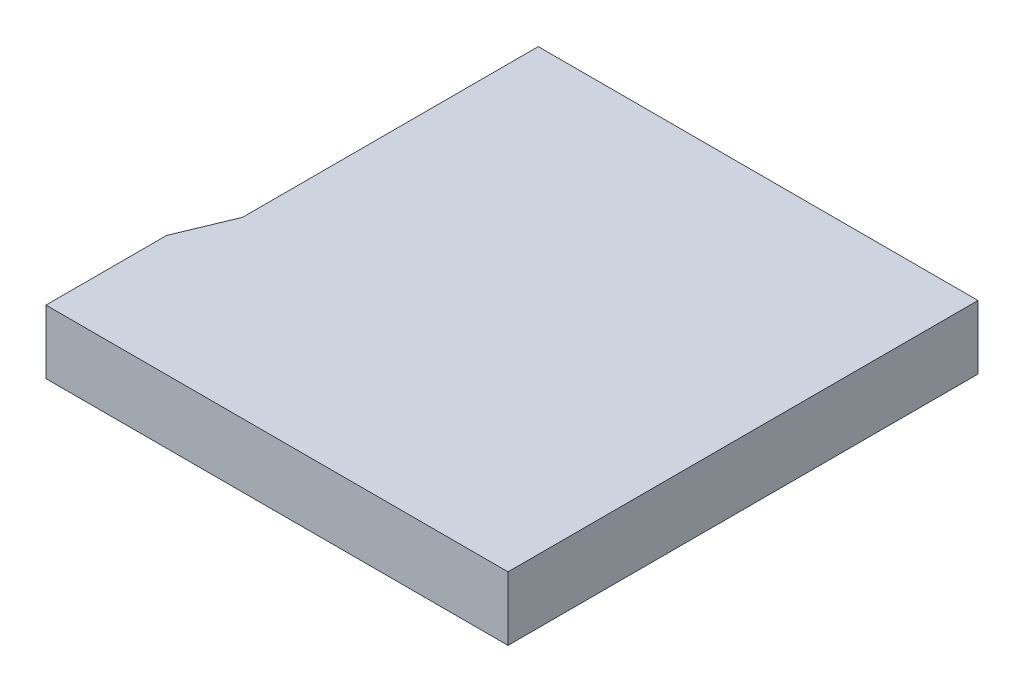
SolidWorks part; units mm, degrees
ref_plane "Спереди" through (0, 0, 0) normal (0, 0, 1) x (1, 0, 0)
ref_plane "Сверху" through (0, 0, 0) normal (0, 1, 0) x (1, 0, 0)
ref_plane "Справа" through (0, 0, 0) normal (1, 0, 0) x (0, 0, -1)
sketch "Эскиз1" plane through (0, 0, 0) normal (0, 1, 0) x (1, 0, 0)
  line L0 (0, 0) -> (14.5, 0)
  line L1 (14.5, 0) -> (14.5, 14.75)
  line L2 (14.5, 14.75) -> (0.6993, 14.75)
  line L3 (0.6993, 14.75) -> (0.6993, 5.4711)
  line L4 (0.6993, 5.4711) -> (0, 3.7867)
  line L5 (0, 3.7867) -> (0, 0)
  point P3 (0, 0.0233)
  dimension "D1" = 14.5
  dimension "D2" = 14.75
extrude "Бобышка-Вытянуть1" add sketch "Эскиз1" along normal blind 2
